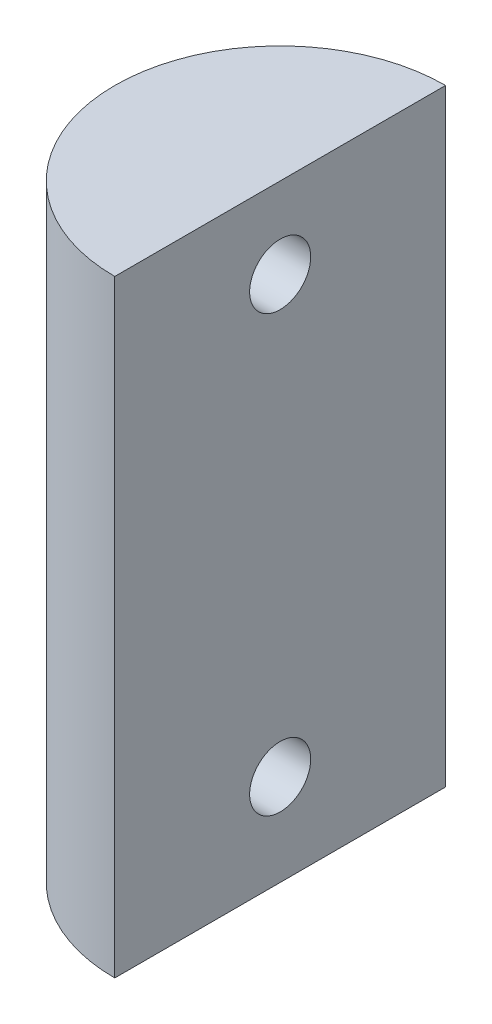
SolidWorks part; units mm, degrees
ref_plane "Front Plane" through (0, 0, 0) normal (0, 0, 1) x (1, 0, 0)
ref_plane "Top Plane" through (0, 0, 0) normal (0, 1, 0) x (1, 0, 0)
ref_plane "Right Plane" through (0, 0, 0) normal (1, 0, 0) x (0, 0, -1)
sketch "Sketch1" plane through (0, 0, 0) normal (0, 1, 0) x (1, 0, 0)
  line L0 (0, 32.5) -> (0, -32.5) construction
  circle A0 centre (0, 0) radius 32.5
  dimension "D1" = 65
extrude "Boss-Extrude1" add sketch "Sketch1" against normal blind 119.376 contours L0 A0
sketch "Sketch2" plane through (0, 0, 0) normal (1, 0, 0) x (0, 0, -1)
  line L0 (0, 0) -> (0, -15.894) construction
  circle A0 centre (0, -15.894) radius 6
  dimension "D2" = 12
  dimension "D1" = 15.894
extrude "Cut-Extrude1" cut sketch "Sketch2" against normal blind 56
sketch "Sketch3" plane through (0, 0, 0) normal (1, 0, 0) x (0, 0, -1)
  line L0 (0, -119.376) -> (0, -101.376) construction
  line L1 (32.5, -119.376) -> (-32.5, -119.376) construction
  circle A0 centre (0, -101.376) radius 6
  dimension "D2" = 12
  dimension "D1" = 18
extrude "Cut-Extrude2" cut sketch "Sketch3" against normal blind 56
